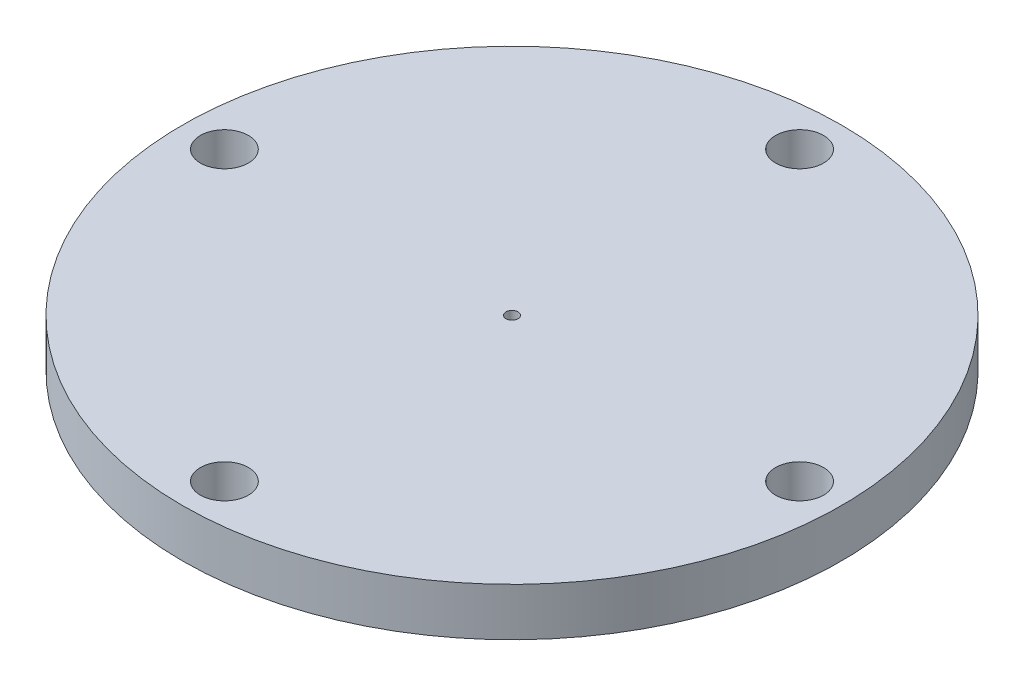
SolidWorks part; units mm, degrees
ref_plane "Front Plane" through (0, 0, 0) normal (0, 0, 1) x (1, 0, 0)
ref_plane "Top Plane" through (0, 0, 0) normal (0, 1, 0) x (1, 0, 0)
ref_plane "Right Plane" through (0, 0, 0) normal (1, 0, 0) x (0, 0, -1)
sketch "Sketch2" plane through (0, 0, 0) normal (0, 1, 0) x (1, 0, 0)
  circle A0 centre (0, 0) radius 27.469
  dimension "D1" = 54.938
extrude "Boss-Extrude1" add sketch "Sketch2" along normal blind 4
sketch "Sketch3" plane through (0, 4, 0) normal (0, 1, 0) x (1, 0, 0)
  circle A1 centre (-23.971, 0) radius 2
  circle A2 centre (0, 23.971) radius 2
  circle A3 centre (23.971, 0) radius 2
  circle A4 centre (0, -23.971) radius 2
  point P14 (0, 0)
  dimension "D2" = 4
  dimension "D1" = 4
extrude "Cut-Extrude1" cut sketch "Sketch3" against normal through all
ref_plane "Plane1" through (0, 5, 0) normal (0, 1, 0) x (1, 0, 0)
sketch "Sketch4" plane through (0, 5, 0) normal (0, 1, 0) x (1, 0, 0)
  circle A0 centre (0, 0) radius 0.5
  dimension "D1" = 1
extrude "Cut-Extrude2" cut sketch "Sketch4" against normal through all
